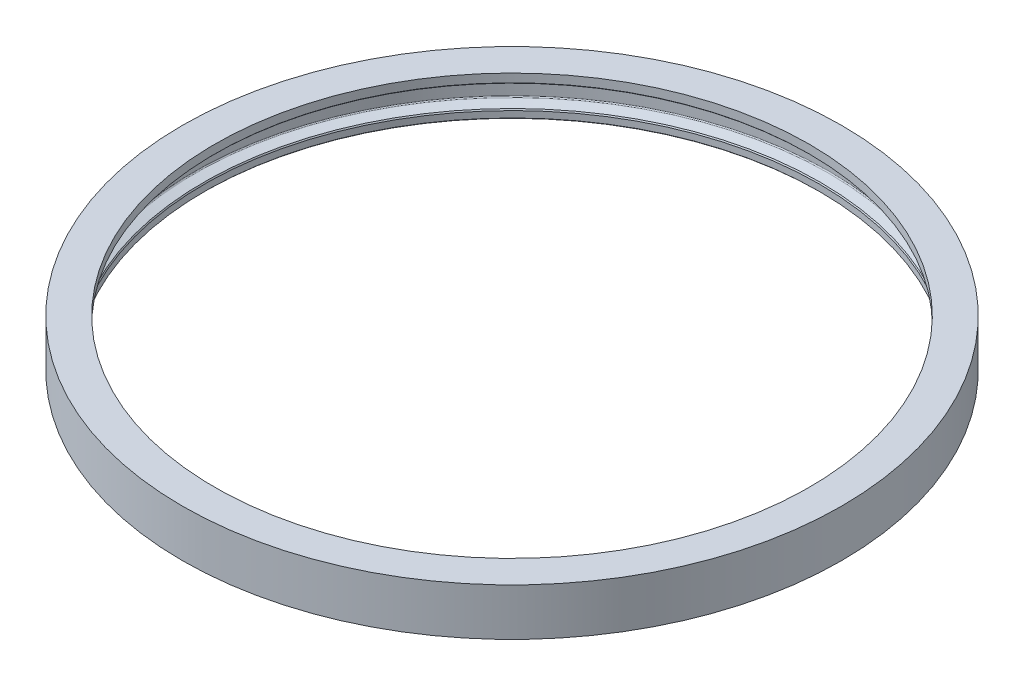
SolidWorks part; units mm, degrees
ref_plane "Front Plane" through (0, 0, 0) normal (0, 0, 1) x (1, 0, 0)
ref_plane "Top Plane" through (0, 0, 0) normal (0, 1, 0) x (1, 0, 0)
ref_plane "Right Plane" through (0, 0, 0) normal (1, 0, 0) x (0, 0, -1)
sketch "Sketch1" plane through (0, 0, 0) normal (1, 0, 0) x (0, 0, -1)
  line L0 (8.255, 9.8559) -> (8.001, 9.6019)
  line L1 (8.001, 9.6019) -> (3.3175, 9.6019)
  line L3 (3, 9.2844) -> (3, 3.3242)
  line L5 (3.2089, 3.0259) -> (5.4418, 2.2132)
  line L6 (5.4418, 2.2132) -> (5.6275, 1.8916)
  line L7 (5.6275, 1.8916) -> (5.6275, 0.254)
  line L8 (5.6275, 0.254) -> (5.3735, 0)
  line L9 (5.3735, 0) -> (0, 0)
  line L11 (0, 12.0097) -> (8.255, 12.0097)
  line L38 (0, 12.0097) -> (0, 0)
  line L39 (0, 6.0049) -> (83.82, 6.0049) construction
  line L40 (83.82, 6.0049) -> (83.82, 9.8559) construction
  line L41 (8.255, 9.8559) -> (8.255, 12.0097)
  arc A2 (3, 9.2844) -> (3.3175, 9.6019) centre (3.3175, 9.2844) cw
  arc A3 (3.2089, 3.0259) -> (3, 3.3242) centre (3.3175, 3.3242) cw
  dimension "D1" = 0.3175
  dimension "D2" = 3
  dimension "D3" = 3.2089
  dimension "D4" = 5.3735
  dimension "D5" = 5.4418
  dimension "D6" = 5.6275
  dimension "D8" = 8.001
  dimension "D9" = 8.255
  dimension "D10" = 83.82
  dimension "D11" = 0.254
  dimension "D12" = 1.8916
  dimension "D13" = 2.2132
  dimension "D14" = 6.0049
  dimension "D15" = 9.6019
sketch "Sketch2" plane through (0, 0, 0) normal (1, 0, 0) x (0, 0, -1)
  line L0 (8.3044, 9.4019) -> (7.5034, 9.4019)
  line L1 (7.5034, 9.4019) -> (3.7034, 7.9019)
  line L2 (3.7034, 7.9019) -> (3.7034, 3.2103)
  line L3 (3.7034, 3.2103) -> (3.889, 2.8888)
  line L4 (3.889, 2.8888) -> (5.9966, 2.1217)
  line L5 (6.3309, 1.6443) -> (6.3309, -1.6443)
  line L6 (5.9966, -2.1217) -> (3.942, -2.8695)
  line L7 (3.942, -2.8695) -> (3.7034, -3.1539)
  line L8 (3.7034, -3.1539) -> (3.7034, -7.9019)
  line L9 (3.7034, -7.9019) -> (7.5034, -9.4019)
  line L10 (7.5034, -9.4019) -> (8.3044, -9.4019)
  line L11 (8.3044, -9.4019) -> (8.3044, 9.4019)
  arc A0 (6.3309, 1.6443) -> (5.9966, 2.1217) centre (5.8229, 1.6443) ccw
  arc A1 (5.9966, -2.1217) -> (6.3309, -1.6443) centre (5.8229, -1.6443) ccw
  dimension "D1" = 0.508
  dimension "D2" = 3.7034
  dimension "D3" = 3.889
  dimension "D4" = 3.942
  dimension "D5" = 5.8229
  dimension "D6" = 5.9966
  dimension "D7" = 1.6443
  dimension "D8" = 7.5034
  dimension "D9" = 8.3044
  dimension "D10" = 3.2103
  dimension "D11" = 7.9019
  dimension "D12" = 9.4019
  dimension "D13" = 1.6443
  dimension "D14" = 7.9019
ref_axis "Axis1" through (0, 6.0049, -83.82) along (0, 1, 0)
revolve "Revolve3" add sketch "Sketch1" angle 360 about axis through (0, 6.0049, -83.82) along (0, 1, 0)
